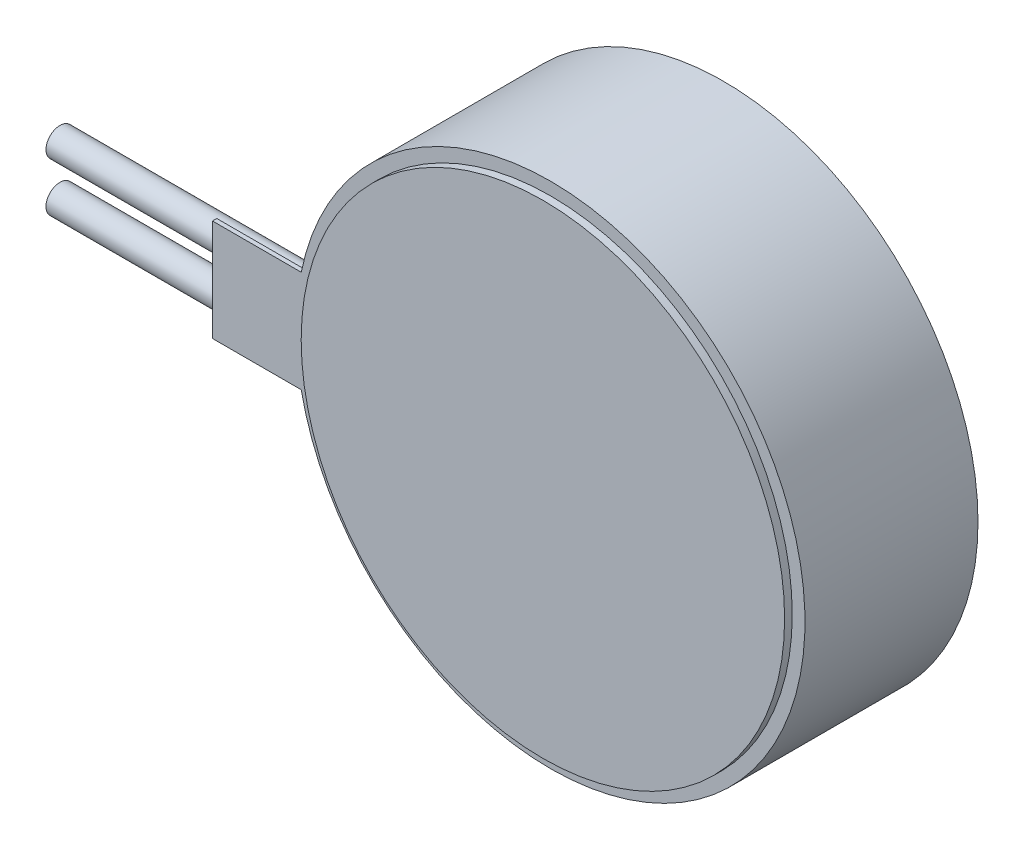
SolidWorks part; units mm, degrees
ref_plane "Front Plane" through (0, 0, 0) normal (0, 0, 1) x (1, 0, 0)
ref_plane "Top Plane" through (0, 0, 0) normal (0, 1, 0) x (1, 0, 0)
ref_plane "Right Plane" through (0, 0, 0) normal (1, 0, 0) x (0, 0, -1)
sketch "Sketch1" plane through (0, 0, 0) normal (0, 0, 1) x (1, 0, 0)
  circle A0 centre (0, 0) radius 5
  dimension "D1" = 10
extrude "Boss-Extrude1" add sketch "Sketch1" along normal blind 3.4 contours A0
sketch "Sketch2" plane through (0, 0, 3.4) normal (0, 0, 1) x (1, 0, 0)
  circle A0 centre (0, 0) radius 4.75
  dimension "D1" = 9.5
extrude "Boss-Extrude2" add sketch "Sketch2" along normal blind 0.15 contours A0
sketch "Sketch4" plane through (0, 0, 3.4) normal (0, 0, 1) x (1, 0, 0)
  line L0 (0, 0) -> (-11.1043, 0) construction
  line L1 (-4.6435, 1) -> (-6.6435, 1)
  line L3 (-4.6435, -1) -> (-6.6435, -1)
  line L4 (-6.6435, 1) -> (-6.6435, -1)
  circle A0 centre (0, 0) radius 4.75 construction
  circle A1 centre (0, 0) radius 4.75 construction
  arc A2 (-4.6435, 1) -> (-4.6435, -1) centre (0, 0) ccw
  point P9 (-6.6435, 0)
extrude "Boss-Extrude3" add sketch "Sketch4" against normal blind 0.085
sketch "Sketch5" plane through (0, 0, 0) normal (1, 0, 0) x (0, 0, -1)
  line L0 (-3.315, -1) -> (-3.315, 1) construction
  circle A0 centre (-3.04, 0.4934) radius 0.275
  circle A1 centre (-3.04, -0.4751) radius 0.275
  dimension "D1" = 0.55
extrude "Boss-Extrude5" add sketch "Sketch5" against normal blind 10 separate body contours A1 | A0
